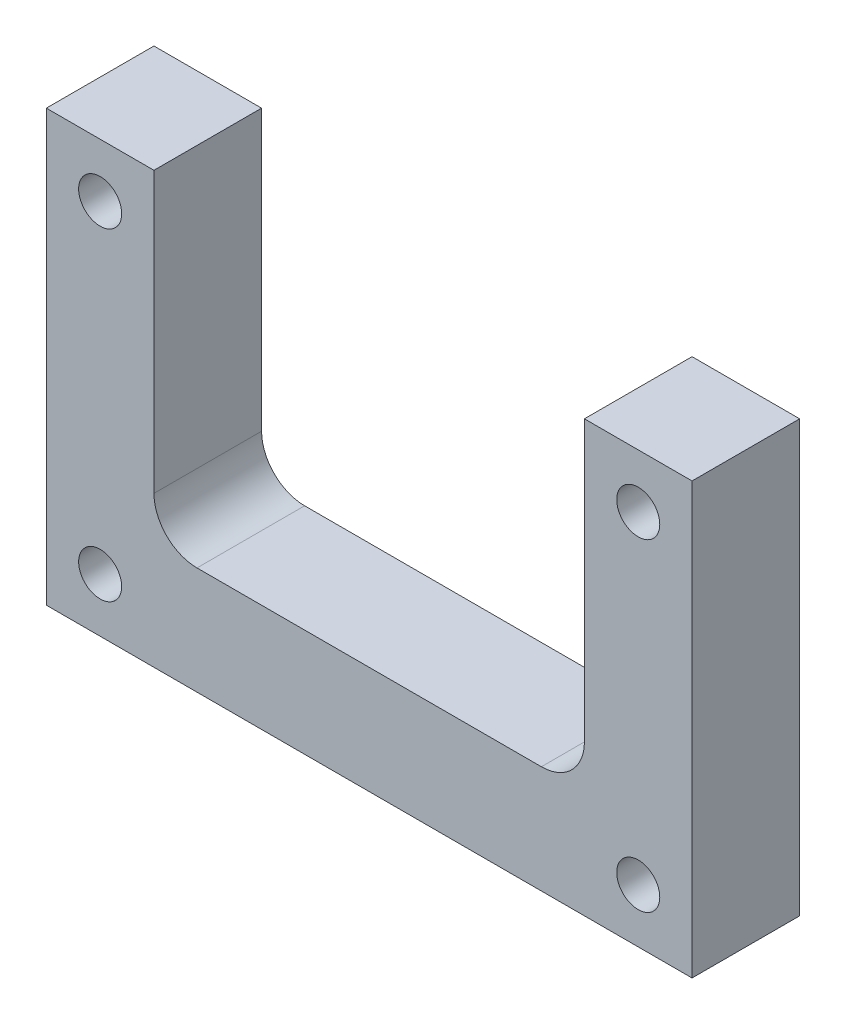
SolidWorks part; units mm, degrees
material "ABS"
ref_plane "Front Plane" through (0, 0, 0) normal (0, 0, 1) x (1, 0, 0)
ref_plane "Top Plane" through (0, 0, 0) normal (0, 1, 0) x (1, 0, 0)
ref_plane "Right Plane" through (0, 0, 0) normal (1, 0, 0) x (0, 0, -1)
sketch "Sketch2" plane through (0, 0, 0) normal (0, 0, 1) x (1, 0, 0)
  line L0 (-25.4, 25.4) -> (-25.4, -12.7)
  line L1 (-38.1, 25.4) -> (-25.4, 25.4)
  line L2 (-38.1, 25.4) -> (-38.1, -25.4)
  line L3 (-38.1, -25.4) -> (38.1, -25.4)
  line L4 (38.1, 25.4) -> (38.1, -25.4)
  line L5 (-38.1, 25.4) -> (38.1, -25.4) construction
  line L6 (-38.1, -25.4) -> (38.1, 25.4) construction
  line L7 (-25.4, -12.7) -> (25.4, -12.7)
  line L8 (25.4, -12.7) -> (25.4, 25.4)
  line L9 (25.4, 25.4) -> (38.1, 25.4)
  line L10 (25.4, -12.7) -> (25.4, -25.4) construction
  point P0 (0, 0)
  dimension "D1" = 76.2
  dimension "D2" = 50.8
  dimension "D3" = 12.7
extrude "Boss-Extrude1" add sketch "Sketch2" along normal blind 12.7
sketch "Sketch4" plane through (0, 0, 0) normal (0, 0, 1) x (1, 0, 0)
  line L0 (-31.75, 19.05) -> (-31.75, -19.05) construction
  line L1 (-31.75, -19.05) -> (31.75, -19.05) construction
  line L2 (31.75, -19.05) -> (31.75, 19.05) construction
  line L3 (31.75, 19.05) -> (-31.75, 19.05) construction
  line L4 (31.75, 19.05) -> (31.75, 25.4) construction
  line L6 (0, -19.05) -> (0, -25.4) construction
  line L7 (-38.1, -25.4) -> (38.1, -25.4) construction
  line L11 (38.1, 25.4) -> (25.4, 25.4) construction
  circle A0 centre (-31.75, 19.05) radius 2.54
  circle A1 centre (-31.75, -19.05) radius 2.54
  circle A2 centre (31.75, -19.05) radius 2.54
  circle A3 centre (31.75, 19.05) radius 2.54
  point P9 (4.4397, -3.4941)
  point P10 (27.1479, 53.9314)
  point P14 (0, -25.4)
  point P17 (31.75, 25.4)
  point P18 (-31.75, 26.8562)
  point P19 (0, 0)
  dimension "D1" = 5.08
  dimension "D2" = 63.5
  dimension "D3" = 38.1
extrude "Cut-Extrude3" cut sketch "Sketch4" along normal through all and the other way through all contours A0 | A3 | A2 | A1
fillet "Fillet1" radius 5.08 2 edges at (25.4, -12.7, 6.35) (-25.4, -12.7, 6.35)
